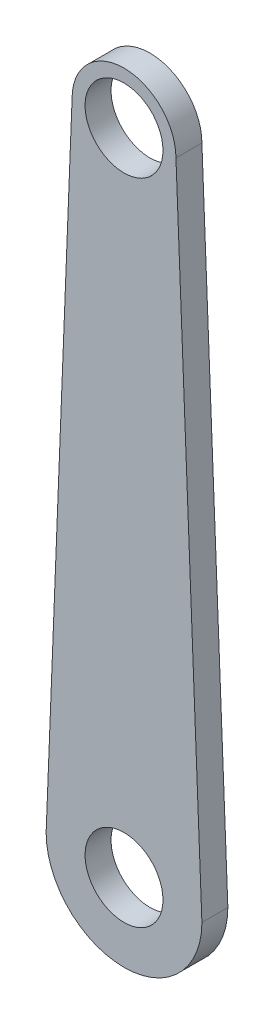
SolidWorks part; units mm, degrees
material "7075-O (SS)"
ref_plane "Płaszczyzna przednia" through (0, 0, 0) normal (0, 0, 1) x (1, 0, 0)
ref_plane "Płaszczyzna górna" through (0, 0, 0) normal (0, 1, 0) x (1, 0, 0)
ref_plane "Płaszczyzna prawa" through (0, 0, 0) normal (1, 0, 0) x (0, 0, -1)
sketch "Szkic1" plane through (0, 0, 0) normal (0, 0, 1) x (1, 0, 0)
  line L0 (8.6909, 15.0061) -> (6.6909, -34.9939)
  line L1 (16.6909, 15.0061) -> (18.6909, -34.9939)
  circle A0 centre (12.6909, 15.0061) radius 3
  arc A1 (16.6909, 15.0061) -> (8.6909, 15.0061) centre (12.6909, 15.0061) ccw
  circle A2 centre (12.6909, -34.9939) radius 3
  arc A3 (6.7101, -34.5146) -> (18.6717, -34.5146) centre (12.6909, -34.9939) ccw
  dimension "D1" = 6
  dimension "D2" = 8
  dimension "D3" = 6
  dimension "D4" = 12
  dimension "D5" = 50
extrude "Dodanie-wyciągnięcie1" add sketch "Szkic1" along normal blind 2 contours L0 A3 L1 A1 A0 A2
